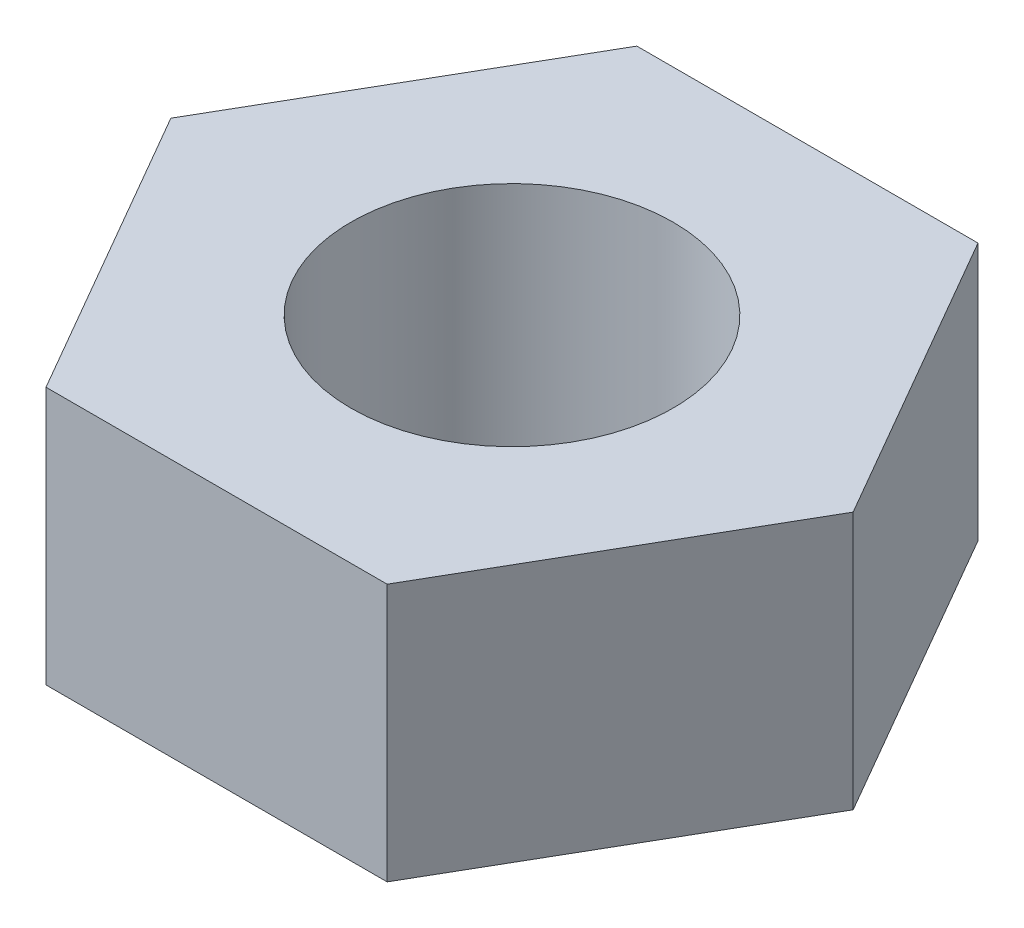
SolidWorks part; units mm, degrees
material "Wrought Stainless Steel"
ref_plane "Front" through (0, 0, 0) normal (0, 0, 1) x (1, 0, 0)
ref_plane "Top" through (0, 0, 0) normal (0, 1, 0) x (1, 0, 0)
ref_plane "Right" through (0, 0, 0) normal (1, 0, 0) x (0, 0, -1)
sketch "Sketch1" plane through (0, 0, 0) normal (0, 1, 0) x (1, 0, 0)
  line L1 (1.5877, -2.75) -> (3.1754, 0)
  line L2 (3.1754, 0) -> (1.5877, 2.75)
  line L3 (1.5877, 2.75) -> (-1.5877, 2.75)
  line L4 (-1.5877, 2.75) -> (-3.1754, 0)
  line L5 (-3.1754, 0) -> (-1.5877, -2.75)
  line L6 (-1.5877, -2.75) -> (1.5877, -2.75)
  circle A0 centre (0, 0) radius 1.5
  circle A1 centre (0, 0) radius 2.75 construction
  dimension "D1" = 3
  dimension "D2" = 5.5
extrude "Extrude1" add sketch "Sketch1" along normal blind 2.4
